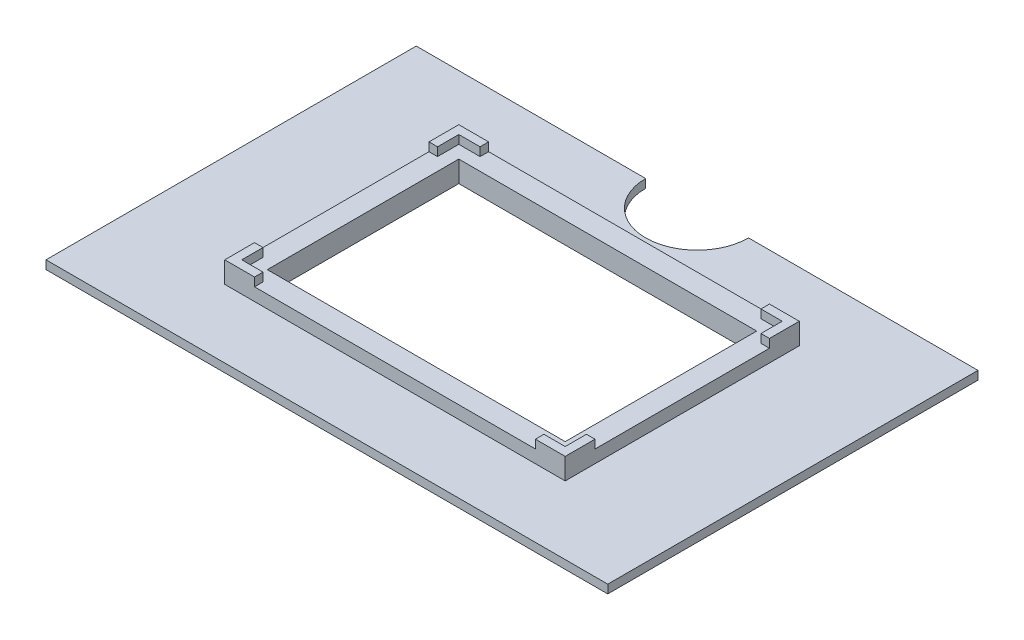
SolidWorks part; units mm, degrees
ref_plane "Front Plane" through (0, 0, 0) normal (0, 0, 1) x (1, 0, 0)
ref_plane "Top Plane" through (0, 0, 0) normal (0, 1, 0) x (1, 0, 0)
ref_plane "Right Plane" through (0, 0, 0) normal (1, 0, 0) x (0, 0, -1)
sketch "Sketch1" plane through (0, 0, 0) normal (0, 1, 0) x (1, 0, 0)
  line L1 (66, -43.5) -> (-66, -43.5)
  line L2 (66, -43.5) -> (66, 43.5)
  line L3 (66, 43.5) -> (-66, 43.5)
  line L4 (-66, -43.5) -> (-66, 43.5)
  line L5 (66, -43.5) -> (-66, 43.5) construction
  line L6 (66, 43.5) -> (-66, -43.5) construction
  point P0 (0, 0)
  dimension "D1" = 132
  dimension "D2" = 87
extrude "Boss-Extrude1" add sketch "Sketch1" along normal blind 2
sketch "Sketch2" plane through (0, 2, 0) normal (0, 1, 0) x (1, 0, 0)
  line L1 (40, -27.5) -> (-40, -27.5)
  line L2 (40, -27.5) -> (40, 27.5)
  line L3 (40, 27.5) -> (-40, 27.5)
  line L4 (-40, -27.5) -> (-40, 27.5)
  line L5 (40, -27.5) -> (-40, 27.5) construction
  line L6 (40, 27.5) -> (-40, -27.5) construction
  point P0 (0, 0)
  dimension "D1" = 80
  dimension "D2" = 55
extrude "Boss-Extrude2" add sketch "Sketch2" along normal blind 5
sketch "Sketch3" plane through (0, 7, 0) normal (0, 1, 0) x (1, 0, 0)
  line L1 (38, -25.5) -> (-38, -25.5)
  line L2 (38, -25.5) -> (38, 25.5)
  line L3 (38, 25.5) -> (-38, 25.5)
  line L4 (-38, -25.5) -> (-38, 25.5)
  line L5 (38, -25.5) -> (-38, 25.5) construction
  line L6 (38, 25.5) -> (-38, -25.5) construction
  point P0 (0, 0)
  dimension "D1" = 76
  dimension "D2" = 51
extrude "Cut-Extrude1" cut sketch "Sketch3" against normal blind 2
sketch "Sketch4" plane through (0, 5, 0) normal (0, 1, 0) x (1, 0, 0)
  line L1 (-35, 22.5) -> (35, 22.5)
  line L2 (-35, 22.5) -> (-35, -22.5)
  line L3 (-35, -22.5) -> (35, -22.5)
  line L4 (35, 22.5) -> (35, -22.5)
  line L5 (-35, 22.5) -> (35, -22.5) construction
  line L6 (-35, -22.5) -> (35, 22.5) construction
  point P0 (0, 0)
  dimension "D1" = 70
  dimension "D2" = 45
extrude "Cut-Extrude2" cut sketch "Sketch4" against normal up to next
sketch "Sketch5" plane through (0, 7, 0) normal (0, 1, 0) x (1, 0, 0)
  line L0 (-38, 25.5) -> (-38, -25.5) construction
  line L1 (-38, 20.5) -> (-40, 20.5)
  line L2 (-38, 20.5) -> (-38, -20.5)
  line L3 (-38, -20.5) -> (-40, -20.5)
  line L4 (-40, 20.5) -> (-40, -20.5)
  line L5 (-40, 27.5) -> (-40, -27.5) construction
  line L6 (40, 27.5) -> (-40, 27.5) construction
  line L7 (-40, -27.5) -> (40, -27.5) construction
  line L8 (0, 25.5) -> (0, -27.5) construction
  line L9 (38, 25.5) -> (-38, 25.5) construction
  line L10 (38, -20.5) -> (40, -20.5)
  line L11 (40, 20.5) -> (40, -20.5)
  line L12 (38, 20.5) -> (38, -20.5)
  line L13 (38, 20.5) -> (40, 20.5)
  line L14 (40, -27.5) -> (40, 27.5) construction
  line L15 (-33, 27.5) -> (33, 27.5)
  line L16 (-33, 27.5) -> (-33, 25.5)
  line L17 (-33, 25.5) -> (33, 25.5)
  line L18 (33, 27.5) -> (33, 25.5)
  line L19 (38, 0) -> (-38, 0) construction
  line L20 (33, -27.5) -> (33, -25.5)
  line L21 (-33, -25.5) -> (33, -25.5)
  line L22 (-33, -27.5) -> (-33, -25.5)
  line L23 (-33, -27.5) -> (33, -27.5)
  dimension "D1" = 7
  dimension "D2" = 7
  dimension "D3" = 7
  dimension "D4" = 7
extrude "Cut-Extrude3" cut sketch "Sketch5" against normal up to surface (2 mm away) up to face at (0, 5, 0)
sketch "Sketch6" plane through (0, 2, 0) normal (0, 1, 0) x (1, 0, 0)
  line L0 (66, 43.5) -> (-66, 43.5) construction
  line L1 (-12.0856, 43.5) -> (12.0856, 43.5)
  arc A0 (-12.0856, 43.5) -> (12.0856, 43.5) centre (0, 43.5) ccw
extrude "Cut-Extrude4" cut sketch "Sketch6" against normal up to surface (2 mm away) up to face at (0, 0, 0)
